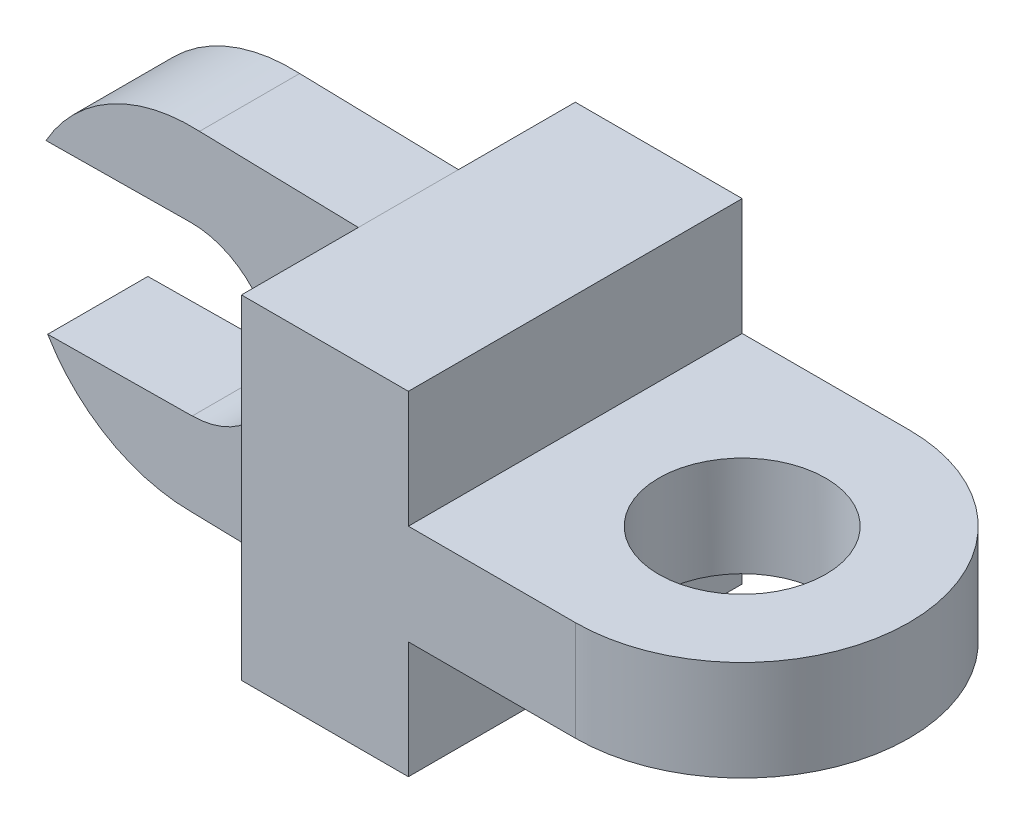
SolidWorks part; units mm, degrees
ref_plane "Front Plane" through (0, 0, 0) normal (0, 0, 1) x (1, 0, 0)
ref_plane "Top Plane" through (0, 0, 0) normal (0, 1, 0) x (1, 0, 0)
ref_plane "Right Plane" through (0, 0, 0) normal (1, 0, 0) x (0, 0, -1)
sketch "Sketch2" plane through (0, 0, 0) normal (0, 1, 0) x (1, 0, 0)
  line L1 (-50, 50) -> (50, 50)
  line L2 (-50, 50) -> (-50, -50)
  line L3 (-50, -50) -> (50, -50)
  arc A0 (50, -50) -> (50, 50) centre (50, 0) ccw
  point P0 (0, 0)
  dimension "D3" = 100
  dimension "D1" = 100
  dimension "D2" = 100
extrude "Boss-Extrude1" add sketch "Sketch2" along normal blind 100 contours A0 L1 L2 L3
sketch "Sketch4" plane through (0, 100, 0) normal (0, 1, 0) x (1, 0, 0)
  circle A0 centre (50, 0) radius 25
  dimension "D1" = 50
extrude "Cut-Extrude2" cut sketch "Sketch4" against normal blind 100
sketch "Sketch6" plane through (0, 0, 50) normal (0, 0, 1) x (1, 0, 0)
  line L0 (100.5203, 35) -> (100.5203, 0)
  line L1 (0, 35) -> (100.5203, 35)
  line L2 (0, 65) -> (100.5203, 65)
  line L3 (100.5203, 0) -> (0, 0)
  line L4 (100.5203, 65) -> (100.5203, 100)
  line L5 (100.5203, 100) -> (0, 100)
  line L10 (0, 65) -> (0, 100)
  line L11 (-50, 100) -> (50, 100) construction
  line L12 (0, 35) -> (0, 0)
extrude "Cut-Extrude4" cut sketch "Sketch6" against normal blind 100
ref_plane "Plane3" through (0, 0, 0) normal (0, 0, 1) x (1, 0, 0)
sketch "Sketch10" plane through (0, 0, 0) normal (0, 0, 1) x (1, 0, 0)
  line L0 (167.3192, 50) -> (-155.7391, 50) construction
  line L1 (-100, 113.1844) -> (-100, -10.7475) construction
  line L2 (100, 35) -> (100, 65) construction
  line L3 (-97.5646, 101.1591) -> (-50, 100)
  line L4 (-50, 0) -> (-100, 1.2184)
  line L5 (-50, 100) -> (-50, 0)
  arc A0 (-97.5646, 101.1591) -> (-100, 1.2184) centre (-100, 51.2184) ccw
  dimension "D2" = 100
  dimension "D1" = 200
extrude "Boss-Extrude3" add sketch "Sketch10" along normal mid plane 30
sketch "Sketch11" plane through (0, 0, 15) normal (0, 0, 1) x (1, 0, 0)
  circle A0 centre (-100, 51.2184) radius 25
  dimension "D1" = 50
extrude "Cut-Extrude5" cut sketch "Sketch11" against normal blind 30
sketch "Sketch12" plane through (0, 0, 15) normal (0, 0, 1) x (1, 0, 0)
  line L1 (-218.8386, 25.0013) -> (-99.7442, 26.2197)
  line L2 (-219.3501, 74.9987) -> (-100.2558, 76.2171)
  line L3 (-100.2558, 76.2171) -> (-99.7442, 26.2197)
  line L4 (-219.3501, 74.9987) -> (-218.8386, 25.0013)
extrude "Cut-Extrude6" cut sketch "Sketch12" against normal blind 30
